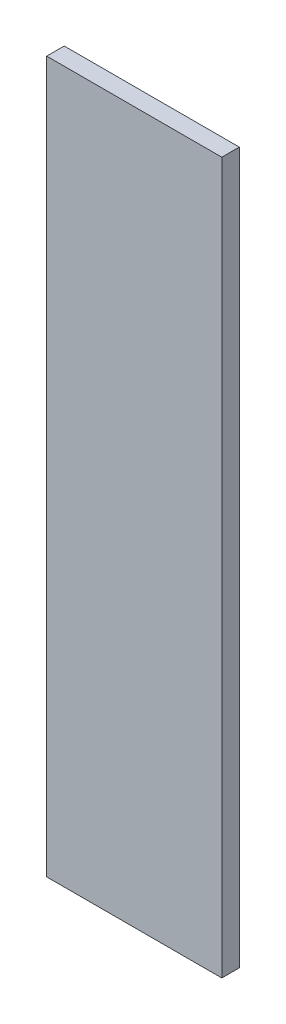
SolidWorks part; units mm, degrees
ref_plane "Front Plane" through (0, 0, 0) normal (0, 0, 1) x (1, 0, 0)
ref_plane "Top Plane" through (0, 0, 0) normal (0, 1, 0) x (1, 0, 0)
ref_plane "Right Plane" through (0, 0, 0) normal (1, 0, 0) x (0, 0, -1)
sketch "Sketch1" plane through (0, 0, 0) normal (0, 0, 1) x (1, 0, 0)
  line L1 (0, 0) -> (250, 0)
  line L2 (0, 0) -> (0, 1015)
  line L3 (0, 1015) -> (250, 1015)
  line L4 (250, 0) -> (250, 1015)
  dimension "D1" = 1015
  dimension "D2" = 250
extrude "Boss-Extrude1" add sketch "Sketch1" along normal blind 25
